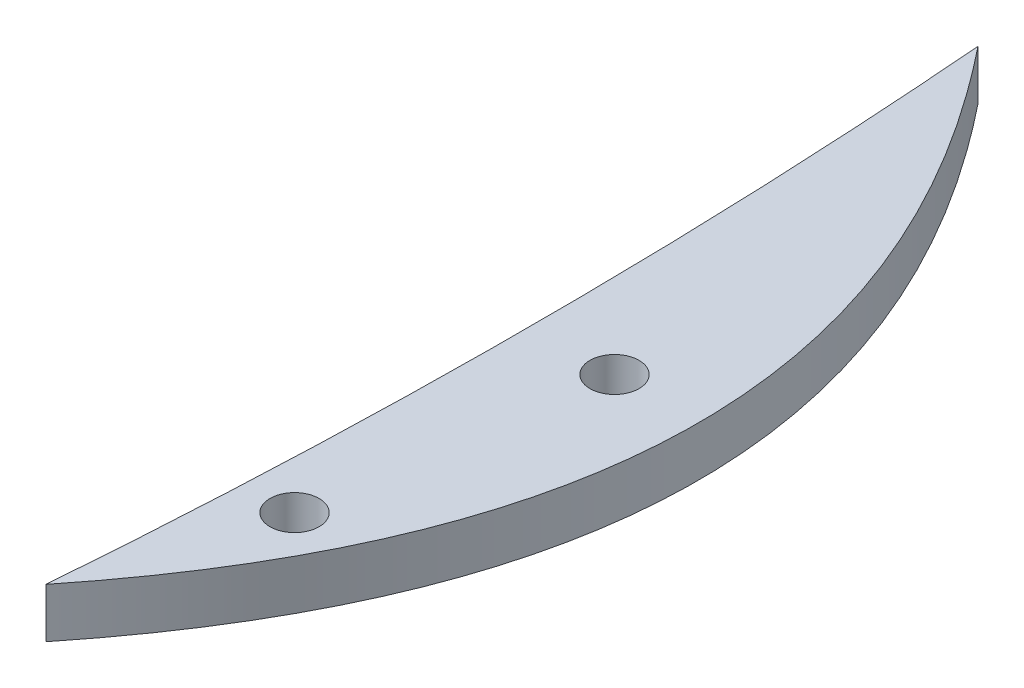
SolidWorks part; units mm, degrees
ref_plane "Front Plane" through (0, 0, 0) normal (0, 0, 1) x (1, 0, 0)
ref_plane "Top Plane" through (0, 0, 0) normal (0, 1, 0) x (1, 0, 0)
ref_plane "Right Plane" through (0, 0, 0) normal (1, 0, 0) x (0, 0, -1)
sketch "Sketch1" plane through (0, 0, 0) normal (0, 1, 0) x (1, 0, 0)
  spline S0 degree 2 poles (-16.834, -19.8456) (13.166, 17.6544) (-16.834, 55.1544) knots 0 0 0 1 1 1
  spline S1 degree 2 poles (-16.834, -19.8456) (-13.834, 17.6544) (-16.834, 55.1544) knots 0 0 0 1 1 1
  dimension "D1" = 75
  dimension "D2" = 37.5
  dimension "D3" = 37.5
  dimension "D4" = 13.5
  dimension "D5" = 1.5
extrude "Boss-Extrude1" add sketch "Sketch1" along normal blind 4 contours S0 S1
sketch "Sketch3" plane through (0, 4, 0) normal (0, 1, 0) x (1, 0, 0)
  circle A2 centre (-8.584, 17.6544) radius 1.975
  circle A3 centre (-11.834, -4.8456) radius 1.975
  dimension "D1" = 3.95
  dimension "D4" = 5
  dimension "D2" = 3.95
  dimension "D3" = 15
extrude "Cut-Extrude1" cut sketch "Sketch3" against normal through all contours A3 | A2
